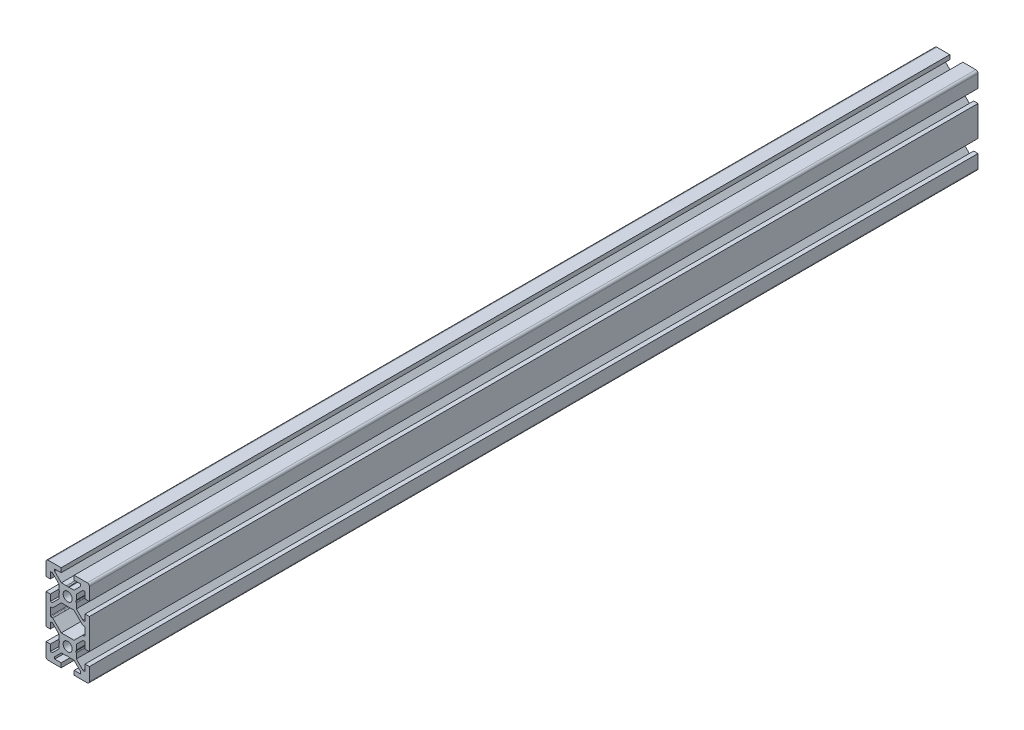
SolidWorks part; units mm, degrees
ref_plane "Front Plane" through (0, 0, 0) normal (0, 0, 1) x (1, 0, 0)
ref_plane "Top Plane" through (0, 0, 0) normal (0, 1, 0) x (1, 0, 0)
ref_plane "Right Plane" through (0, 0, 0) normal (1, 0, 0) x (0, 0, -1)
ref_plane "Plane1" through (0, 0, 0) normal (0, 0, 1) x (1, 0, 0)
sketch "Sketch1" plane through (0, 0, 0) normal (0, 0, 1) x (1, 0, 0)
  line L0 (-9, -20) -> (-3, -20)
  line L1 (-3, -20) -> (-3, -18)
  line L2 (-3, -18) -> (-6, -18)
  line L3 (-6, -18) -> (-6, -17.0607)
  line L4 (-6, -17.0607) -> (-2.9393, -14)
  line L5 (-2.9393, -14) -> (-2.5, -14)
  line L8 (-0.4036, -13.933) -> (0, -13.7)
  line L9 (0, -13.7) -> (0.4036, -13.933)
  line L10 (0.6536, -14) -> (2.9393, -14)
  line L11 (2.9393, -14) -> (6, -17.0607)
  line L12 (6, -17.0607) -> (6, -18)
  line L13 (6, -18) -> (3, -18)
  line L14 (3, -18) -> (3, -20)
  line L15 (3, -20) -> (9, -20)
  line L16 (10, -19) -> (10, -13)
  line L17 (10, -13) -> (8, -13)
  line L18 (8, -13) -> (8, -16)
  line L19 (8, -16) -> (7.0607, -16)
  line L20 (7.0607, -16) -> (4, -12.9393)
  line L21 (4, -12.9393) -> (4, -12.5)
  line L24 (3.933, -10.4036) -> (3.7, -10)
  line L25 (3.7, -10) -> (3.933, -9.5964)
  line L26 (4, -9.3464) -> (4, -7.0607)
  line L27 (4, -7.0607) -> (7.0607, -4)
  line L28 (7.0607, -4) -> (8, -4)
  line L29 (8, -4) -> (8, -7)
  line L30 (8, -7) -> (10, -7)
  line L31 (10, -7) -> (10, 7)
  line L32 (10, 7) -> (8, 7)
  line L33 (8, 7) -> (8, 4)
  line L34 (8, 4) -> (7.0607, 4)
  line L35 (7.0607, 4) -> (4, 7.0607)
  line L36 (4, 7.0607) -> (4, 9.3464)
  line L37 (3.933, 9.5964) -> (3.7, 10)
  line L38 (3.7, 10) -> (3.933, 10.4036)
  line L39 (-4, -7.5) -> (-4, -9.3464)
  line L40 (-2.5, -14) -> (-0.6536, -14)
  line L41 (4, 12.5) -> (4, 12.9393)
  line L42 (4, 12.9393) -> (7.0607, 16)
  line L43 (7.0607, 16) -> (8, 16)
  line L44 (8, 16) -> (8, 13)
  line L45 (8, 13) -> (10, 13)
  line L46 (10, 13) -> (10, 19)
  line L47 (9, 20) -> (3, 20)
  line L48 (3, 20) -> (3, 18)
  line L49 (3, 18) -> (6, 18)
  line L50 (6, 18) -> (6, 17.0607)
  line L51 (6, 17.0607) -> (2.9393, 14)
  line L52 (2.9393, 14) -> (0.6536, 14)
  line L53 (0.4036, 13.933) -> (0, 13.7)
  line L54 (0, 13.7) -> (-0.4036, 13.933)
  line L55 (-2.5, 14) -> (-0.6536, 14)
  line L56 (4, 12.5) -> (4, 10.6536)
  line L57 (-2.5, 14) -> (-2.9393, 14)
  line L58 (-2.9393, 14) -> (-6, 17.0607)
  line L59 (-6, 17.0607) -> (-6, 18)
  line L60 (-6, 18) -> (-3, 18)
  line L61 (-3, 18) -> (-3, 20)
  line L62 (-3, 20) -> (-9, 20)
  line L63 (-10, 19) -> (-10, 13)
  line L64 (-10, 13) -> (-8, 13)
  line L65 (-8, 13) -> (-8, 16)
  line L66 (-8, 16) -> (-7.0607, 16)
  line L67 (-7.0607, 16) -> (-4, 12.9393)
  line L68 (-4, 12.9393) -> (-4, 10.6536)
  line L69 (-3.933, 10.4036) -> (-3.7, 10)
  line L70 (-3.7, 10) -> (-3.933, 9.5964)
  line L71 (4, -12.5) -> (4, -10.6536)
  line L73 (-4, 7.5) -> (-4, 7.0607)
  line L74 (-4, 7.0607) -> (-7.0607, 4)
  line L75 (-7.0607, 4) -> (-8, 4)
  line L76 (-8, 4) -> (-8, 7)
  line L77 (-8, 7) -> (-10, 7)
  line L78 (-10, 7) -> (-10, -7)
  line L79 (-10, -7) -> (-8, -7)
  line L80 (-8, -7) -> (-8, -4)
  line L81 (-8, -4) -> (-7.0607, -4)
  line L82 (-7.0607, -4) -> (-4, -7.0607)
  line L83 (-4, -7.0607) -> (-4, -7.5)
  line L86 (-3.933, -9.5964) -> (-3.7, -10)
  line L87 (-3.7, -10) -> (-3.933, -10.4036)
  line L88 (-4, -10.6536) -> (-4, -12.9393)
  line L89 (-4, -12.9393) -> (-7.0607, -16)
  line L90 (-7.0607, -16) -> (-8, -16)
  line L91 (-8, -16) -> (-8, -13)
  line L92 (-8, -13) -> (-10, -13)
  line L93 (-10, -13) -> (-10, -19)
  line L94 (-7.7, -2) -> (-7.0636, -2)
  line L95 (-6.8515, -2.0879) -> (-2.9393, -6)
  line L96 (-2.9393, -6) -> (2.9393, -6)
  line L97 (2.9393, -6) -> (6.8515, -2.0879)
  line L98 (7.0636, -2) -> (7.7, -2)
  line L99 (8, -1.7) -> (8, 1.7)
  line L100 (7.7, 2) -> (7.0636, 2)
  line L101 (6.8515, 2.0879) -> (2.9393, 6)
  line L102 (2.9393, 6) -> (-2.9393, 6)
  line L103 (-2.9393, 6) -> (-6.8515, 2.0879)
  line L104 (-7.0636, 2) -> (-7.7, 2)
  line L105 (-8, 1.7) -> (-8, -1.7)
  line L106 (-4, 9.3464) -> (-4, 7.5)
  arc A0 (-10, -19) -> (-9, -20) centre (-9, -19) ccw
  arc A1 (-0.6536, -14) -> (-0.4036, -13.933) centre (-0.6536, -13.5) ccw
  arc A2 (0.4036, -13.933) -> (0.6536, -14) centre (0.6536, -13.5) ccw
  arc A3 (9, -20) -> (10, -19) centre (9, -19) ccw
  arc A4 (4, -10.6536) -> (3.933, -10.4036) centre (3.5, -10.6536) ccw
  arc A5 (3.933, -9.5964) -> (4, -9.3464) centre (3.5, -9.3464) ccw
  arc A6 (4, 9.3464) -> (3.933, 9.5964) centre (3.5, 9.3464) ccw
  arc A7 (3.933, 10.4036) -> (4, 10.6536) centre (3.5, 10.6536) ccw
  arc A8 (10, 19) -> (9, 20) centre (9, 19) ccw
  arc A9 (0.6536, 14) -> (0.4036, 13.933) centre (0.6536, 13.5) ccw
  arc A10 (-0.4036, 13.933) -> (-0.6536, 14) centre (-0.6536, 13.5) ccw
  arc A11 (-9, 20) -> (-10, 19) centre (-9, 19) ccw
  arc A12 (-4, 10.6536) -> (-3.933, 10.4036) centre (-3.5, 10.6536) ccw
  arc A13 (-3.933, 9.5964) -> (-4, 9.3464) centre (-3.5, 9.3464) ccw
  arc A14 (-4, -9.3464) -> (-3.933, -9.5964) centre (-3.5, -9.3464) ccw
  arc A15 (-3.933, -10.4036) -> (-4, -10.6536) centre (-3.5, -10.6536) ccw
  arc A16 (-8, -1.7) -> (-7.7, -2) centre (-7.7, -1.7) ccw
  arc A17 (-7.0636, -2) -> (-6.8515, -2.0879) centre (-7.0636, -2.3) cw
  arc A18 (6.8515, -2.0879) -> (7.0636, -2) centre (7.0636, -2.3) cw
  arc A19 (7.7, -2) -> (8, -1.7) centre (7.7, -1.7) ccw
  arc A20 (8, 1.7) -> (7.7, 2) centre (7.7, 1.7) ccw
  arc A21 (7.0636, 2) -> (6.8515, 2.0879) centre (7.0636, 2.3) cw
  arc A22 (-6.8515, 2.0879) -> (-7.0636, 2) centre (-7.0636, 2.3) cw
  arc A23 (-7.7, 2) -> (-8, 1.7) centre (-7.7, 1.7) ccw
extrude "Boss-Extrude1" add sketch "Sketch1" against normal blind 410
ref_plane "Plane2" through (0, 0, 0) normal (1, 0, 0) x (0, 0, -1)
sketch "Sketch2" plane through (0, 0, 0) normal (1, 0, 0) x (0, 0, -1)
  line L0 (0, 10) -> (0, 12.1)
  line L1 (0, 12.1) -> (1200, 12.1)
  line L2 (1200, 12.1) -> (1200, 10)
  line L3 (1200, 10) -> (0, 10)
  line L4 (1200, 10) -> (0, 10) construction
revolve "Cut-Revolve1" cut sketch "Sketch2" angle 360 about L4
ref_plane "Plane3" through (0, 0, 0) normal (1, 0, 0) x (0, 0, -1)
sketch "Sketch3" plane through (0, 0, 0) normal (1, 0, 0) x (0, 0, -1)
  line L0 (0, -10) -> (0, -7.9)
  line L1 (0, -7.9) -> (1200, -7.9)
  line L2 (1200, -7.9) -> (1200, -10)
  line L3 (1200, -10) -> (0, -10)
  line L4 (1200, -10) -> (0, -10) construction
revolve "Cut-Revolve2" cut sketch "Sketch3" angle 360 about L4
